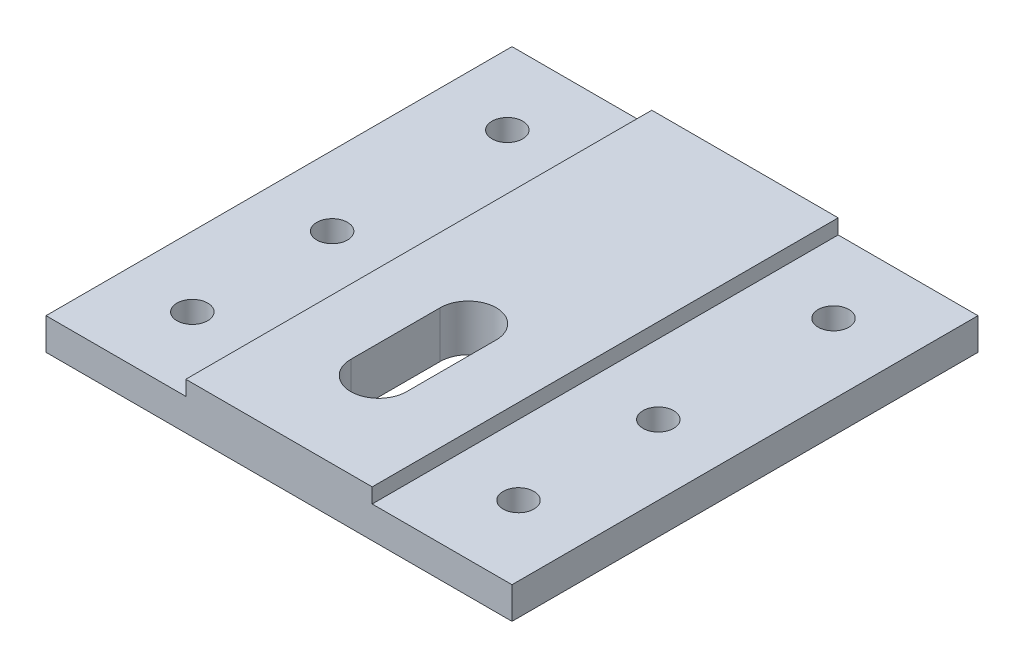
SolidWorks part; units mm, degrees
ref_plane "Front Plane" through (0, 0, 0) normal (0, 0, 1) x (1, 0, 0)
ref_plane "Top Plane" through (0, 0, 0) normal (0, 1, 0) x (1, 0, 0)
ref_plane "Right Plane" through (0, 0, 0) normal (1, 0, 0) x (0, 0, -1)
sketch "Sketch2" plane through (0, 0, 0) normal (0, 1, 0) x (1, 0, 0)
  line L1 (63.5, -63.5) -> (-63.5, -63.5)
  line L2 (63.5, -63.5) -> (63.5, 63.5)
  line L3 (63.5, 63.5) -> (-63.5, 63.5)
  line L4 (-63.5, -63.5) -> (-63.5, 63.5)
  line L5 (63.5, -63.5) -> (-63.5, 63.5) construction
  line L6 (63.5, 63.5) -> (-63.5, -63.5) construction
  point P0 (0, 0)
  dimension "D1" = 127
  dimension "D2" = 127
extrude "Boss-Extrude1" add sketch "Sketch2" along normal blind 12.7
sketch "Sketch3" plane through (0, 0, 63.5) normal (0, 0, 1) x (1, 0, 0)
  line L1 (-63.5, 12.7) -> (-25.4, 12.7)
  line L2 (-63.5, 12.7) -> (-63.5, 8.6584)
  line L3 (-63.5, 8.6584) -> (-25.4, 8.6584)
  line L4 (-25.4, 12.7) -> (-25.4, 8.6584)
  line L5 (63.5, 12.7) -> (25.4, 12.7)
  line L6 (63.5, 12.7) -> (63.5, 8.6584)
  line L7 (63.5, 8.6584) -> (25.4, 8.6584)
  line L8 (25.4, 12.7) -> (25.4, 8.6584)
  dimension "D1" = 38.1
  dimension "D2" = 38.1
  dimension "D3" = 50.8
extrude "Cut-Extrude2" cut sketch "Sketch3" against normal through all
hole_wizard "Ø10.0mm Dowel Hole1" positions "Sketch8" profile "Sketch9" hole size "Ø10.0" standard "ANSI Metric" end condition through all
sketch "Sketch8" plane through (0, 0, 0) normal (0, -1, 0) x (-1, 0, 0)
  line L0 (-63.5, 63.5) -> (63.5, 63.5) construction
  line L1 (-44.45, -63.5) -> (-44.45, 63.5) construction
  line L2 (63.5, -63.5) -> (-63.5, -63.5) construction
  line L3 (44.45, -63.5) -> (44.45, 63.5) construction
  point P0 (-44.45, 43.18)
  point P2 (-44.45, -4.572)
  point P4 (-44.45, -42.672)
  point P6 (44.45, 43.18)
  point P8 (44.45, -4.572)
  point P10 (44.45, -42.672)
  point P33 (48.26, 42.418)
  point P34 (48.26, -43.8404)
  dimension "D1" = 47.752
  dimension "D2" = 38.1
  dimension "D3" = 20.32
  dimension "D4" = 47.752
  dimension "D5" = 20.32
  dimension "D6" = 38.1
  dimension "D7" = 19.05
  dimension "D8" = 19.05
sketch "Sketch9" plane through (44.45, 0, -43.18) normal (1, 0, 0) x (0, 0, -1)
  line L0 (0, 0) -> (0, 12.7)
  line L1 (0, 12.7) -> (4.191, 12.7)
  line L2 (4.191, 12.7) -> (4.191, 0)
  line L5 (4.191, 0) -> (0, 0)
  line L11 (0, -6.35) -> (0, 107.95) construction
  dimension "Thru Hole Dia." = 8.382
  dimension "Thru Hole Depth" = 12.7
sketch "Sketch10" plane through (0, 0, 0) normal (0, -1, 0) x (-1, 0, 0)
  line L0 (0, -11.938) -> (0, -36.322) construction
  line L1 (7.62, -11.938) -> (7.62, -36.322)
  line L2 (-7.62, -11.938) -> (-7.62, -36.322)
  line L3 (63.5, -63.5) -> (-63.5, -63.5) construction
  arc A0 (7.62, -11.938) -> (-7.62, -11.938) centre (0, -11.938) ccw
  arc A1 (-7.62, -36.322) -> (7.62, -36.322) centre (0, -36.322) ccw
  point P3 (0, -24.13)
  point P8 (0, -43.942)
  point P9 (0, -4.318)
  dimension "D1" = 15.24
  dimension "D2" = 39.624
  dimension "D3" = 19.558
extrude "Cut-Extrude4" cut sketch "Sketch10" against normal through all contours L2 A1 L1 A0
equation "\"D2@Sketch2\"=\"D1@Sketch2\""
equation "\"D4@Sketch8\"=\"D1@Sketch8\""
equation "\"D5@Sketch8\"=\"D3@Sketch8\""
equation "\"D6@Sketch8\"=\"D2@Sketch8\""
